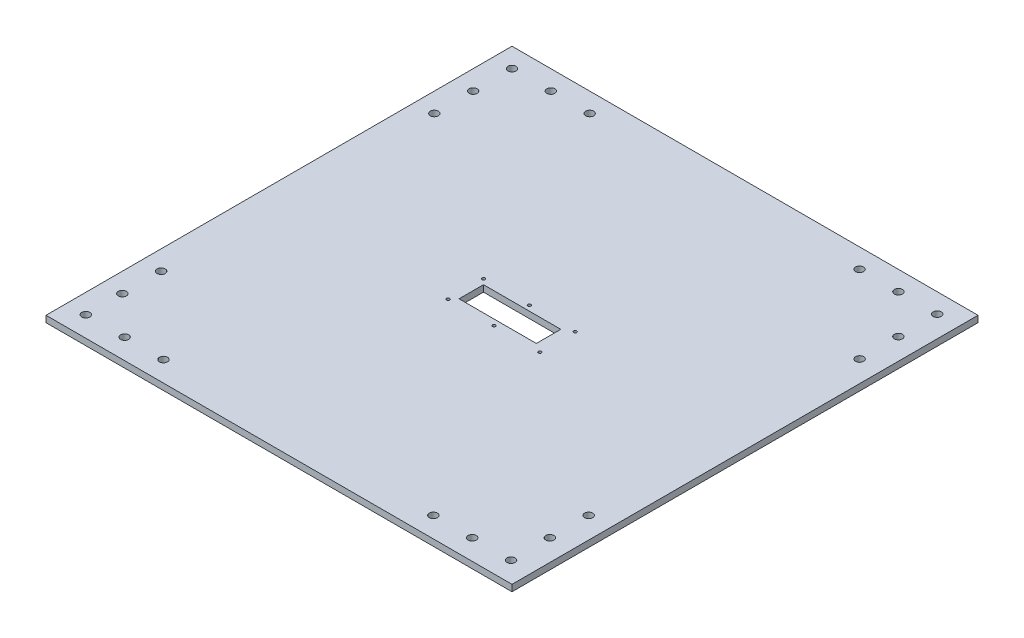
SolidWorks part; units mm, degrees
ref_plane "Front Plane" through (0, 0, 0) normal (0, 0, 1) x (1, 0, 0)
ref_plane "Top Plane" through (0, 0, 0) normal (0, 1, 0) x (1, 0, 0)
ref_plane "Right Plane" through (0, 0, 0) normal (1, 0, 0) x (0, 0, -1)
sketch "Sketch2" plane through (0, 0, 0) normal (0, 1, 0) x (1, 0, 0)
  line L0 (109.7173, 396.7683) -> (109.7173, -60.4317) construction
  line L1 (-118.8827, 164.7341) -> (338.3173, 168.1683) construction
  line L2 (338.3173, -60.4317) -> (-118.8827, -60.4317)
  line L3 (338.3173, -60.4317) -> (338.3173, 396.7683)
  line L4 (338.3173, 396.7683) -> (-118.8827, 396.7683)
  line L5 (-118.8827, -60.4317) -> (-118.8827, 396.7683)
  line L6 (59.7174, 190.1683) -> (159.7172, 190.1683) construction
  line L11 (59.7174, 190.1683) -> (59.7174, 146.1683) construction
  line L16 (159.7172, 190.1683) -> (159.7172, 146.1683) construction
  line L17 (59.7174, 146.1683) -> (159.7172, 146.1683) construction
  line L18 (-118.8827, 355.0694) -> (-98.8827, 355.0694) construction
  line L19 (-99.8327, 377.7183) -> (317.3673, 377.7183) construction
  line L20 (69.7504, 156.1683) -> (145.605, 156.1683)
  line L21 (145.605, 156.1683) -> (145.605, 180.1683)
  line L22 (145.605, 180.1683) -> (69.7504, 180.1683)
  line L23 (69.7504, 180.1683) -> (69.7504, 156.1683)
  line L24 (-71.2276, 396.7683) -> (-71.2276, 377.7183) construction
  line L25 (317.3673, 377.7183) -> (317.3673, -40.4317) construction
  line L26 (317.3673, -40.4317) -> (-99.8327, -40.4317) construction
  line L27 (-99.8327, -40.4317) -> (-99.8327, 377.7183) construction
  line L28 (64.7339, 185.216) -> (154.7007, 185.216) construction
  line L29 (-99.8327, 377.7183) -> (-61.7327, 377.7183) construction
  line L30 (154.7007, 185.216) -> (154.7007, 150.5186) construction
  line L31 (154.7007, 150.5186) -> (64.7339, 150.5186) construction
  line L32 (64.7339, 150.5186) -> (64.7339, 185.216) construction
  line L33 (-61.7327, 377.7183) -> (-23.6327, 377.7183) construction
  line L34 (-99.8327, 377.7183) -> (-99.8327, 339.6183) construction
  line L35 (-99.8327, 339.6183) -> (-99.8327, 301.5183) construction
  line L36 (317.3673, 377.7183) -> (279.2673, 377.7183) construction
  line L37 (279.2673, 377.7183) -> (241.1673, 377.7183) construction
  line L38 (317.3673, 377.7183) -> (317.3673, 339.6183) construction
  line L39 (317.3673, 339.6183) -> (317.3673, 301.5183) construction
  line L40 (317.3673, -40.4317) -> (317.3673, -2.3317) construction
  line L41 (317.3673, -2.3317) -> (317.3673, 35.7683) construction
  line L42 (317.3673, -40.4317) -> (279.2673, -40.4317) construction
  line L43 (279.2673, -40.4317) -> (241.1673, -40.4317) construction
  line L44 (-99.8327, -40.4317) -> (-61.7327, -40.4317) construction
  line L45 (-61.7327, -40.4317) -> (-23.6327, -40.4317) construction
  line L46 (-99.8327, -40.4317) -> (-99.8327, -4.6163) construction
  line L47 (-99.8327, -4.6163) -> (-99.8327, 33.4837) construction
  circle A0 centre (154.7007, 185.216) radius 1.5
  circle A1 centre (154.7007, 150.5186) radius 1.5
  circle A2 centre (64.7339, 150.5186) radius 1.5
  circle A3 centre (64.7339, 185.216) radius 1.5
  circle A4 centre (-99.8327, 377.7183) radius 3.9688
  circle A5 centre (317.3673, 377.7183) radius 3.9688
  circle A6 centre (-99.8327, -40.4317) radius 3.9688
  circle A7 centre (317.3673, -40.4317) radius 3.9688
  circle A10 centre (109.7173, 185.216) radius 1.5
  circle A12 centre (109.7173, 150.5186) radius 1.5
  circle A13 centre (-61.7327, 377.7183) radius 3.9688
  circle A14 centre (-23.6327, 377.7183) radius 3.9688
  circle A15 centre (-99.8327, 339.6183) radius 3.9688
  circle A16 centre (-99.8327, 301.5183) radius 3.9688
  circle A17 centre (241.1673, 377.7183) radius 3.9687
  circle A18 centre (279.2673, 377.7183) radius 3.9688
  circle A19 centre (317.3673, 339.6183) radius 3.9688
  circle A20 centre (317.3673, 301.5183) radius 3.9688
  circle A21 centre (317.3673, -2.3317) radius 3.9688
  circle A22 centre (317.3673, 35.7683) radius 3.9688
  circle A23 centre (279.2673, -40.4317) radius 3.9688
  circle A24 centre (241.1673, -40.4317) radius 3.9687
  circle A25 centre (-61.7327, -40.4317) radius 3.9687
  circle A26 centre (-23.6327, -40.4317) radius 3.9688
  circle A27 centre (-99.8327, -4.6163) radius 3.9688
  circle A28 centre (-99.8327, 33.4837) radius 3.9688
  point P26 (64.7339, 185.216)
  dimension "D7" = 7.9375
  dimension "D8" = 7.9375
  dimension "D9" = 7.9375
  dimension "D10" = 7.9375
  dimension "D11" = 3
  dimension "D12" = 3
  dimension "D1" = 457.2
  dimension "D2" = 457.2
  dimension "D3" = 24
  dimension "D4" = 75.8545
  dimension "D5" = 5.0165
  dimension "D6" = 4.9522
  dimension "D13" = 19.05
  dimension "D14" = 19.05
extrude "Boss-Extrude1" add sketch "Sketch2" along normal blind 6.35
